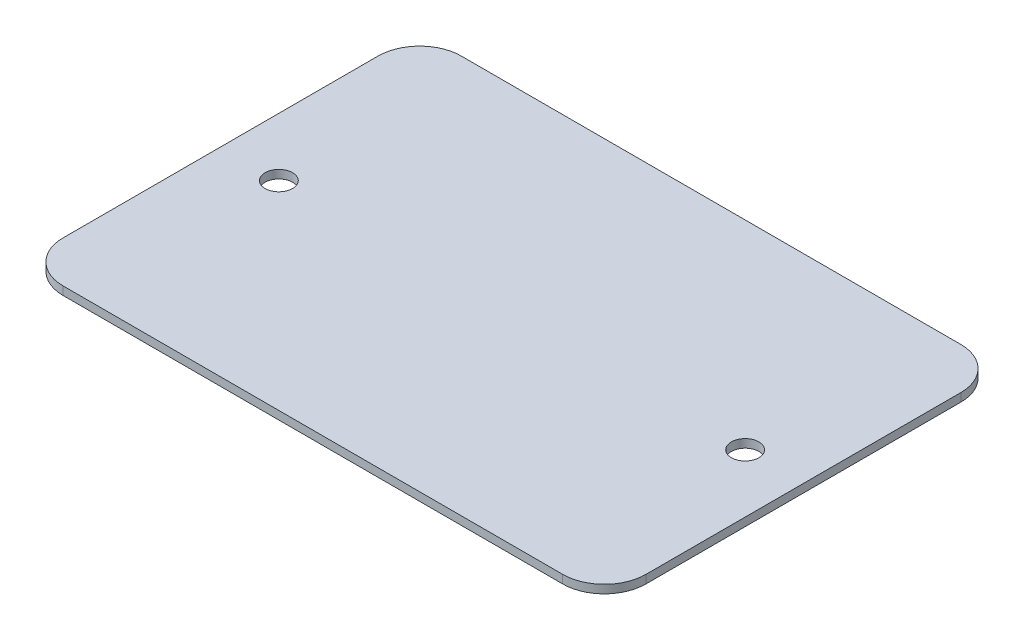
SolidWorks part; units mm, degrees
ref_plane "Alzado" through (0, 0, 0) normal (0, 0, 1) x (1, 0, 0)
ref_plane "Planta" through (0, 0, 0) normal (0, 1, 0) x (1, 0, 0)
ref_plane "Vista lateral" through (0, 0, 0) normal (1, 0, 0) x (0, 0, -1)
sketch "Croquis1" plane through (0, 0, 0) normal (0, 1, 0) x (1, 0, 0)
  line L0 (-63.897, 12.3114) -> (-63.897, -35.5093)
  line L1 (-63.897, -35.5093) -> (6.103, -35.5093)
  line L2 (6.103, -35.5093) -> (6.103, 12.3114)
  line L3 (6.103, 12.3114) -> (-63.897, 12.3114)
  line L4 (-63.897, -35.5093) -> (-52.4687, -35.5093)
extrude "Saliente-Extruir1" add sketch "Croquis1" along normal blind 1 contours L2 L3 L0 L1
sketch "Croquis2" plane through (0, 1, 0) normal (0, 1, 0) x (1, 0, 0)
  line L0 (6.103, 12.3114) -> (6.103, -11.599)
  line L1 (6.103, -35.5093) -> (6.103, 12.3114) construction
  line L2 (6.103, -11.599) -> (-0.897, -11.599)
  line L3 (-63.897, 12.3114) -> (-63.897, -11.599)
  line L4 (-63.897, 12.3114) -> (-63.897, -35.5093) construction
  line L5 (-63.897, -11.599) -> (-56.897, -11.599)
fillet "Redondeo1" radius 5 4 edges at (6.103, 0.5, -12.3114) (-63.897, 0.5, -12.3114) (-63.897, 0.5, 35.5093) (6.103, 0.5, 35.5093)
hole_wizard "Taladro roscado M41" positions "Croquis4" profile "Croquis3" tap size "M4" standard "ISO"
sketch "Croquis4" plane through (0, 1, 0) normal (0, 1, 0) x (1, 0, 0)
  line L0 (-63.897, 7.3114) -> (-63.897, -30.5093) construction
  line L1 (6.103, -30.5093) -> (6.103, 7.3114) construction
  point P0 (-56.897, -11.599)
  point P2 (-0.897, -11.599)
  dimension "D1" = 7
  dimension "D2" = 7
sketch "Croquis3" plane through (-56.897, 1, 11.599) normal (1, 0, 0) x (0, 0, 1)
  line L0 (0, 0) -> (0, 12.4914)
  line L1 (0, 12.4914) -> (1.65, 11.5)
  line L2 (1.65, 11.5) -> (1.65, 0)
  line L5 (1.65, 0) -> (0, 0)
  line L10 (0, 12.4914) -> (-1.65, 11.5) construction
  line L11 (0, -6.35) -> (0, 107.95) construction
  dimension "Diámetro de perforador para roscar" = 3.3
  dimension "Profundidad de perforador para roscar" = 11.5
  dimension "Ángulo de perforador" = 118
cosmetic thread "Rosca de taladro1" parameters "D1"=1, "D2"=4
cosmetic thread "Rosca de taladro2" parameters "D1"=1, "D2"=4
